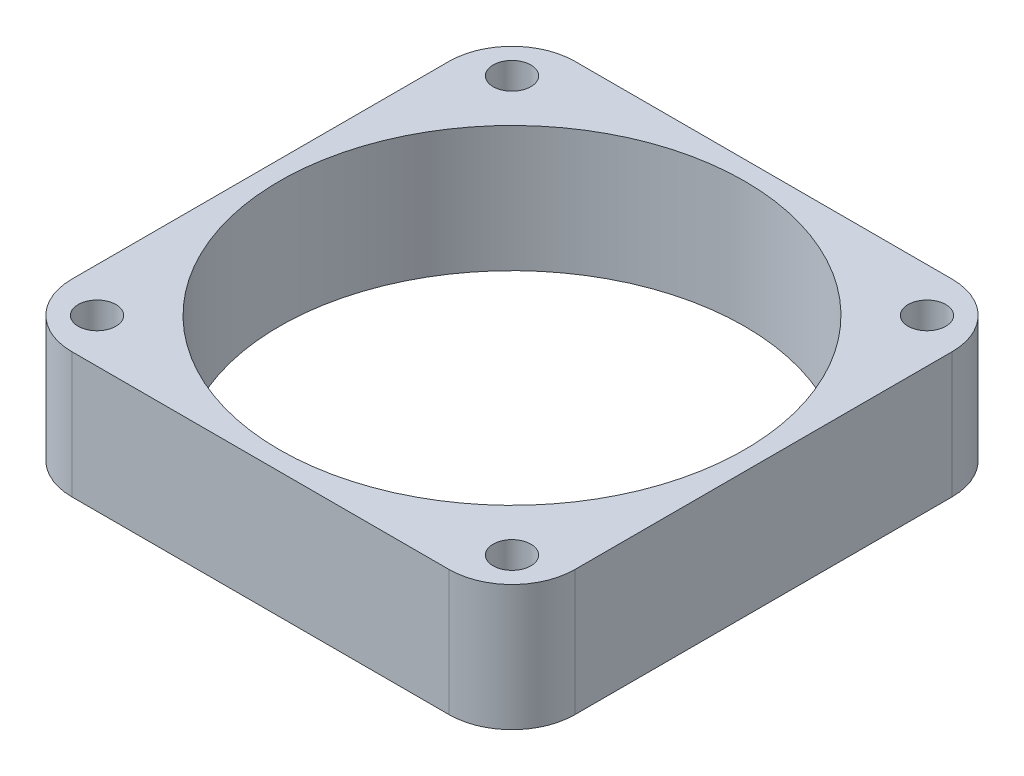
SolidWorks part; units mm, degrees
ref_plane "Front" through (0, 0, 0) normal (0, 0, 1) x (1, 0, 0)
ref_plane "Top" through (0, 0, 0) normal (0, 1, 0) x (1, 0, 0)
ref_plane "Right" through (0, 0, 0) normal (1, 0, 0) x (0, 0, -1)
sketch "Sketch1" plane through (0, 0, 0) normal (0, 1, 0) x (1, 0, 0)
  line L1 (-20, -20) -> (20, -20)
  line L2 (-20, -20) -> (-20, 20)
  line L3 (-20, 20) -> (20, 20)
  line L4 (20, -20) -> (20, 20)
  line L5 (-20, -20) -> (20, 20) construction
  line L6 (-20, 20) -> (20, -20) construction
  point P0 (0, 0)
  dimension "D1" = 40
extrude "Boss-Extrude1" add sketch "Sketch1" along normal blind 10
fillet "Fillet1" radius 5 4 edges at (-20, 5, -20) (20, 5, -20) (-20, 5, 20) (20, 5, 20)
sketch "Sketch2" plane through (0, 10, 0) normal (0, 1, 0) x (1, 0, 0)
  circle A0 centre (0, 0) radius 18.5
  dimension "D1" = 37
extrude "Cut-Extrude1" cut sketch "Sketch2" against normal through all
sketch "Sketch3" plane through (0, 10, 0) normal (0, 1, 0) x (1, 0, 0)
  line L0 (0, 20) -> (0, -20) construction
  line L1 (15, 20) -> (-15, 20) construction
  line L2 (-15, -20) -> (15, -20) construction
  line L3 (20, 0) -> (-20, 0) construction
  line L4 (20, -15) -> (20, 15) construction
  line L5 (-20, 15) -> (-20, -15) construction
  circle A0 centre (-16.5, 16.5) radius 1.5
  circle A1 centre (16.5, 16.5) radius 1.5
  circle A2 centre (16.5, -16.5) radius 1.5
  circle A3 centre (-16.5, -16.5) radius 1.5
  dimension "D1" = 3
  dimension "D2" = 16.5
  dimension "D3" = 16.5
extrude "Cut-Extrude2" cut sketch "Sketch3" against normal through all
